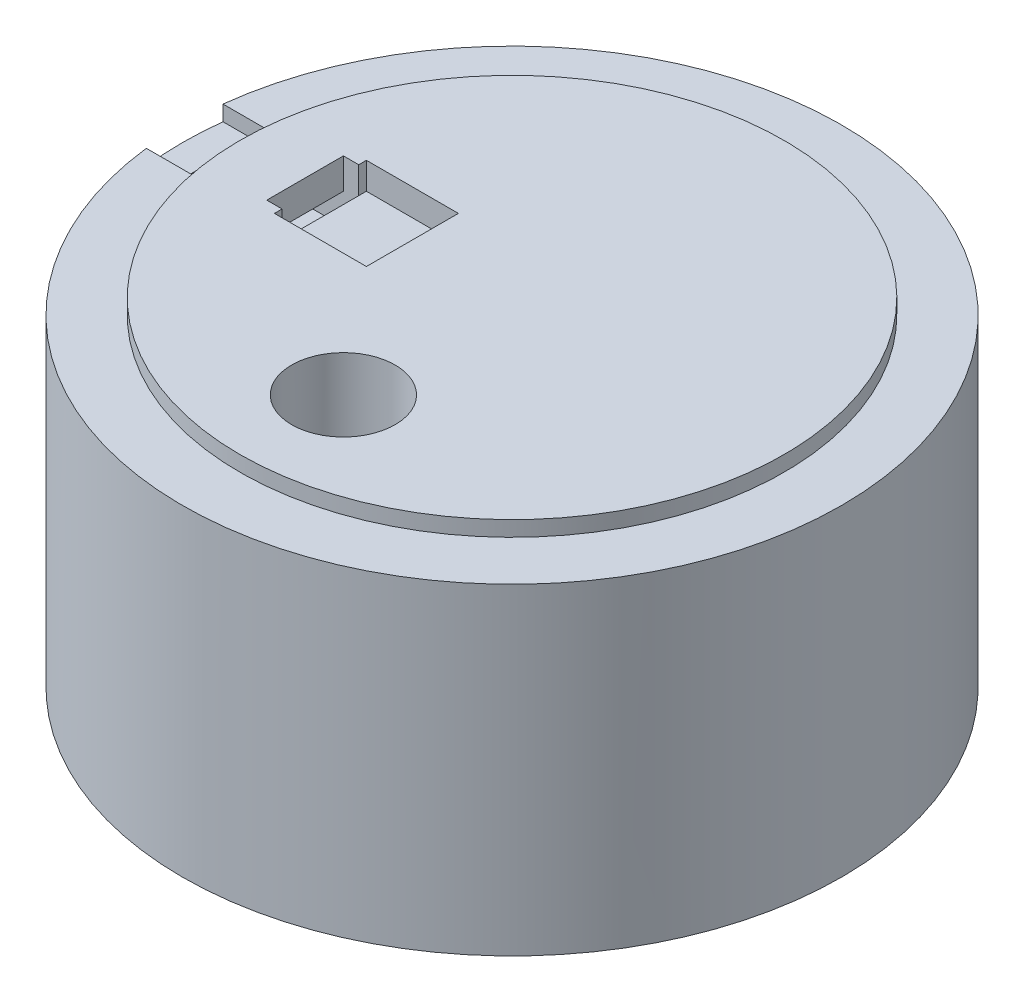
SolidWorks part; units mm, degrees
ref_plane "Front Plane" through (0, 0, 0) normal (0, 0, 1) x (1, 0, 0)
ref_plane "Top Plane" through (0, 0, 0) normal (0, 1, 0) x (1, 0, 0)
ref_plane "Right Plane" through (0, 0, 0) normal (1, 0, 0) x (0, 0, -1)
sketch "Sketch2" plane through (0, 0, 0) normal (0, 1, 0) x (1, 0, 0)
  circle A0 centre (0, 0) radius 43
  dimension "D1" = 86
extrude "Boss-Extrude1" add sketch "Sketch2" along normal blind 42
sketch "Sketch3" plane through (0, 42, 0) normal (0, 1, 0) x (1, 0, 0)
  circle A0 centre (0, 0) radius 35.5
  dimension "D1" = 71
extrude "Boss-Extrude2" add sketch "Sketch3" along normal blind 2
sketch "Sketch4" plane through (0, 0, 0) normal (0, -1, 0) x (1, 0, 0)
  line L0 (0, 43) -> (0, 0) construction
  line L1 (-3.5, 32.8139) -> (-3.5, 37.5)
  line L2 (-3.5, 37.5) -> (3.5, 37.5)
  line L3 (3.5, 37.5) -> (3.5, 32.8139)
  line L4 (30.1676, -13.3758) -> (34.226, -15.7189)
  line L5 (34.226, -15.7189) -> (30.726, -21.7811)
  line L6 (30.726, -21.7811) -> (26.6676, -19.438)
  line L7 (-26.6676, -19.438) -> (-30.726, -21.7811)
  line L8 (-30.726, -21.7811) -> (-34.226, -15.7189)
  line L9 (-34.226, -15.7189) -> (-30.1676, -13.3758)
  arc A0 (-3.5, 32.8139) -> (-30.1676, -13.3758) centre (0, 0) ccw
  circle A1 centre (0, 0) radius 43 construction
  arc A2 (30.1676, -13.3758) -> (3.5, 32.8139) centre (0, 0) ccw
  arc A3 (-26.6676, -19.438) -> (26.6676, -19.438) centre (0, 0) ccw
  point P21 (0, 0)
  dimension "D1" = 66
  dimension "D2" = 7
  dimension "D3" = 37.5
  dimension "D4" = 3
extrude "Cut-Extrude1" cut sketch "Sketch4" against normal blind 30
sketch "Sketch5" plane through (0, 44, 0) normal (0, 1, 0) x (1, 0, 0)
  line L5 (0, 0) -> (-43, 0) construction
  line L7 (-27, 5) -> (-25, 5)
  line L8 (-27, 5) -> (-27, -5)
  line L9 (-27, -5) -> (-25, -5)
  line L10 (-25, 5) -> (-25, -5)
  circle A1 centre (0, 0) radius 43 construction
  dimension "D3" = 25
  dimension "D4" = 2
  dimension "D5" = 10
sketch "Sketch6" plane through (0, 44, 0) normal (0, 1, 0) x (1, 0, 0)
  line L0 (-25, 6) -> (-13, -6) construction
  line L1 (-25, 6) -> (-13, 6)
  line L2 (-25, 6) -> (-25, -6)
  line L3 (-25, -6) -> (-13, -6)
  line L4 (-13, 6) -> (-13, -6)
  point P4 (-13, 0)
  point P6 (-19, 0)
  dimension "D1" = 12
  dimension "D2" = 12
  dimension "D3" = 19
extrude "Cut-Extrude2" cut sketch "Sketch6" against normal blind 3.5
extrude "Cut-Extrude3" cut sketch "Sketch5" against normal blind 8
sketch "Sketch7" plane through (0, 44, 0) normal (0, 1, 0) x (1, 0, 0)
  circle A0 centre (0, -22) radius 6.75
  dimension "D1" = 13.5
  dimension "D2" = 22
extrude "Cut-Extrude4" cut sketch "Sketch7" against normal blind 14
sketch "Sketch8" plane through (0, 42, 0) normal (0, 1, 0) x (1, 0, 0)
  line L0 (0, 0) -> (-43, 0) construction
  line L1 (-42.7083, 5) -> (-35.1461, 5)
  line L2 (-42.7083, -5) -> (-35.1461, -5)
  arc A0 (-42.7083, 5) -> (-42.7083, -5) centre (0, 0) ccw
  arc A1 (-35.1461, 5) -> (-35.1461, -5) centre (0, 0) ccw
  dimension "D2" = 71
  dimension "D3" = 86
  dimension "D1" = 10
extrude "Cut-Extrude5" cut sketch "Sketch8" against normal blind 2
sketch "Sketch9" plane through (0, 40, 0) normal (0, 1, 0) x (1, 0, 0)
  line L0 (-35.1461, 5) -> (-38.9272, 5)
  line L1 (-35.1461, 5) -> (-42.7083, 5) construction
  line L2 (-38.9272, 5) -> (-38.9272, -5)
  line L3 (-42.7083, -5) -> (-35.1461, -5) construction
  line L4 (-38.9272, -5) -> (-35.1461, -5)
  arc A0 (-35.1461, 5) -> (-35.1461, -5) centre (0, 0) ccw
extrude "Cut-Extrude6" cut sketch "Sketch9" against normal blind 41
sketch "Sketch10" plane through (-27, 0, 0) normal (1, 0, 0) x (0, 0, -1)
  line L1 (-5, 40) -> (5, 40)
  line L2 (-5, 40) -> (-5, 36)
  line L3 (-5, 36) -> (5, 36)
  line L4 (5, 40) -> (5, 36)
extrude "Cut-Extrude7" cut sketch "Sketch10" against normal blind 10
sketch "Sketch11" plane through (0, 30, 0) normal (0, -1, 0) x (1, 0, 0)
  line L0 (-6.75, 22) -> (6.75, 22) construction
  circle A2 centre (0, 22) radius 6.75 construction
  circle A3 centre (0, 22) radius 6.75
  circle A4 centre (0, 22) radius 8.75
  dimension "D1" = 13.5
  dimension "D2" = 17.5
extrude "Boss-Extrude3" add sketch "Sketch11" along normal blind 2
equation "\"D3@Sketch5\"=19+6"
